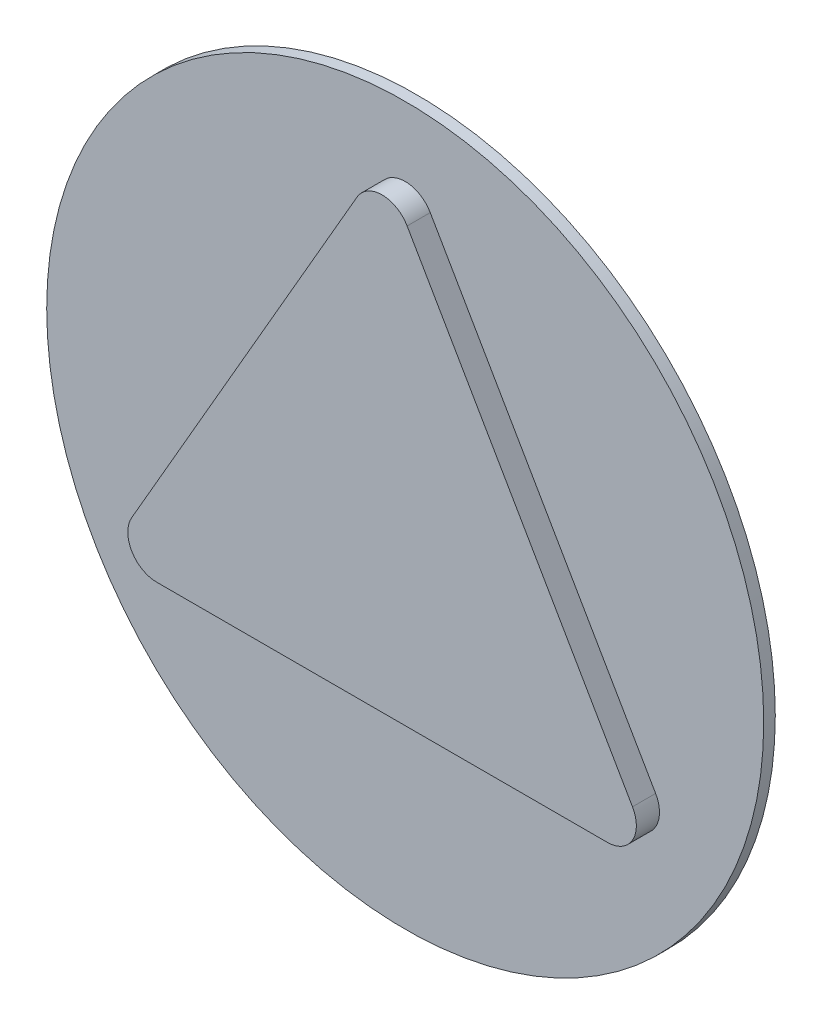
SolidWorks part; units mm, degrees
ref_plane "Front Plane" through (0, 0, 0) normal (0, 0, 1) x (1, 0, 0)
ref_plane "Top Plane" through (0, 0, 0) normal (0, 1, 0) x (1, 0, 0)
ref_plane "Right Plane" through (0, 0, 0) normal (1, 0, 0) x (0, 0, -1)
sketch "Sketch1" plane through (0, 0, 0) normal (0, 0, 1) x (1, 0, 0)
  circle A0 centre (0, 0) radius 15.5
  dimension "D1" = 31
extrude "Boss-Extrude1" add sketch "Sketch1" along normal blind 0.5 contours A0
sketch "Sketch2" plane through (0, 0, 0.5) normal (0, 0, 1) x (1, 0, 0)
  line L1 (-11.9078, -6.875) -> (11.9078, -6.875)
  line L2 (11.9078, -6.875) -> (0, 13.75)
  line L3 (0, 13.75) -> (-11.9078, -6.875)
  circle A0 centre (0, 0) radius 13.75 construction
  dimension "D1" = 27.5
extrude "Boss-Extrude2" add sketch "Sketch2" along normal blind 1
fillet "Fillet1" radius 1.25 3 edges at (11.9078, -6.875, 1) (-11.9078, -6.875, 1) (0, 13.75, 1)
